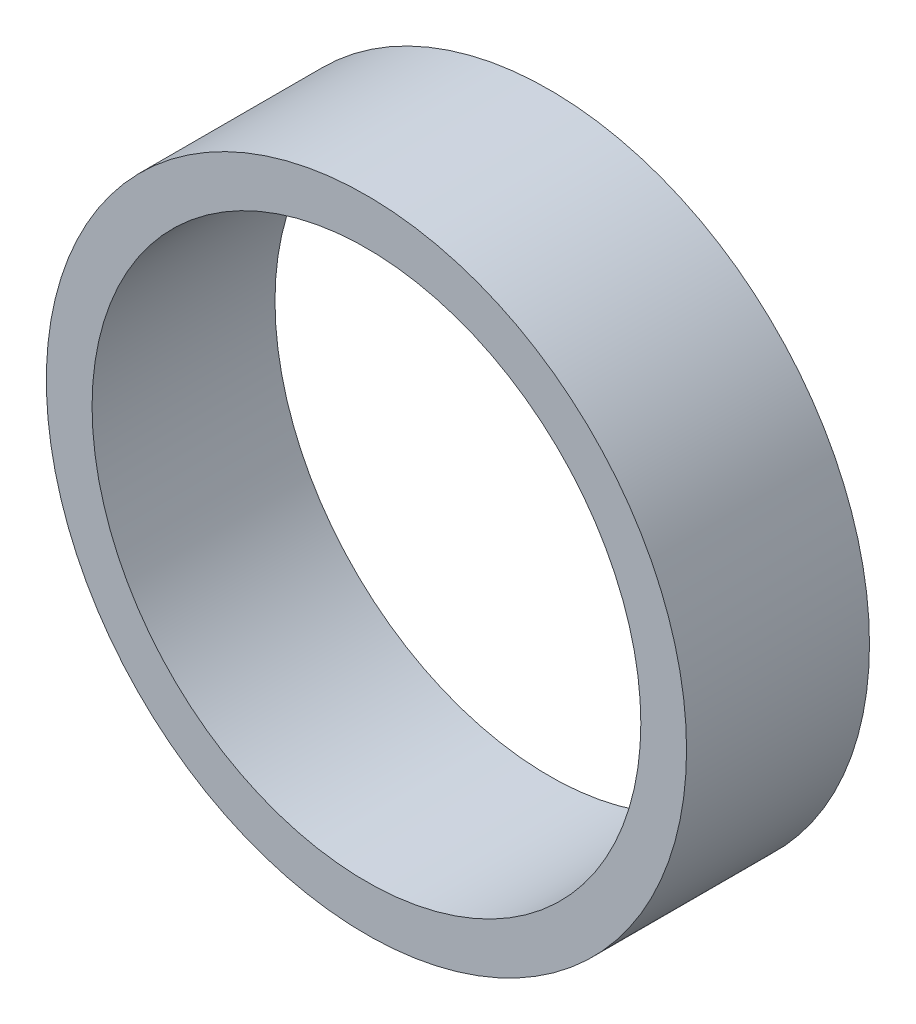
SolidWorks part; units mm, degrees
material "PTFE (general)"
ref_plane "Front Plane" through (0, 0, 0) normal (0, 0, 1) x (1, 0, 0)
ref_plane "Top Plane" through (0, 0, 0) normal (0, 1, 0) x (1, 0, 0)
ref_plane "Right Plane" through (0, 0, 0) normal (1, 0, 0) x (0, 0, -1)
sketch "Sketch1" plane through (0, 0, 0) normal (0, 0, 1) x (1, 0, 0)
  circle A0 centre (0, 0) radius 3
  circle A1 centre (0, 0) radius 3.5
extrude "Boss-Extrude1" add sketch "Sketch1" along normal blind 2
